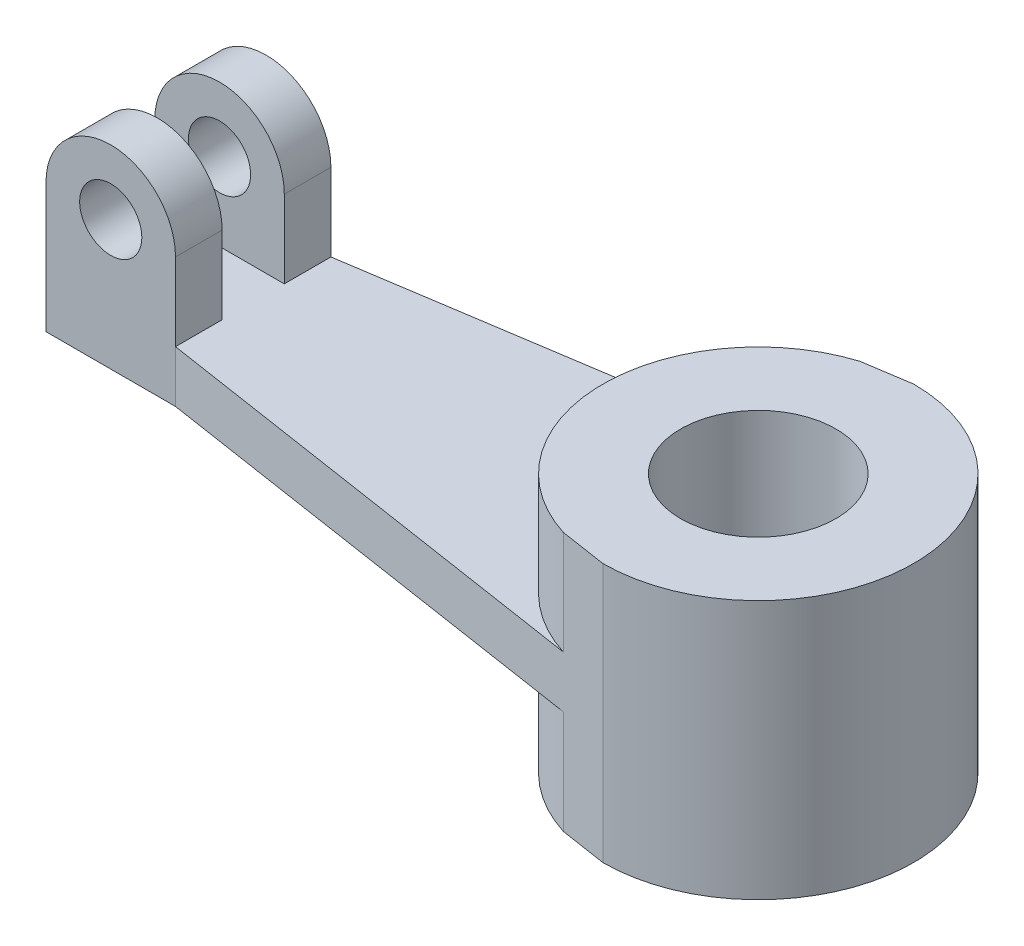
SolidWorks part; units mm, degrees
ref_plane "Front" through (0, 0, 0) normal (0, 0, 1) x (1, 0, 0)
ref_plane "Top" through (0, 0, 0) normal (0, 1, 0) x (1, 0, 0)
ref_plane "Right" through (0, 0, 0) normal (1, 0, 0) x (0, 0, -1)
sketch "Sketch1" plane through (0, 0, 0) normal (0, 1, 0) x (1, 0, 0)
  line L0 (-97.5, 15) -> (-122.5, 15)
  line L1 (-122.5, 15) -> (-122.5, -15)
  line L2 (-122.5, -15) -> (-97.5, -15)
  line L3 (-97.5, -15) -> (0, -30)
  line L4 (-97.5, 15) -> (0, 30)
  circle A0 centre (0, 0) radius 30
  point P4 (0, 0)
  point P9 (0, 0)
  point P10 (0, 0)
  point P11 (0, 0)
  point P13 (0, 30)
  point P14 (0, 0)
  point P15 (-110, 15)
  point P16 (-97.5, 14.942)
  point P17 (-122.5, 0)
  dimension "D1" = 30
  dimension "D2" = 30
  dimension "D3" = 25
  dimension "D4" = 110
extrude "Boss-Extrude2" add sketch "Sketch1" along normal blind 10 contours A0 L4 L0 L1 L2 L3 | L3 A0 L4
sketch "Sketch3" plane through (0, 10, 0) normal (0, 1, 0) x (1, 0, 0)
  line L0 (-97.5, 15) -> (-97.5, 6)
  line L1 (-97.5, 6) -> (-122.5, 6)
  line L2 (-122.5, 15) -> (-122.5, -15) construction
  line L3 (-122.5, 6) -> (-122.5, 15)
  line L4 (-122.5, 15) -> (-97.5, 15)
  line L5 (-97.5, -15) -> (-97.5, -6)
  line L6 (-97.5, -6) -> (-122.5, -6)
  line L7 (-122.5, -6) -> (-122.5, -15)
  line L8 (-122.5, -15) -> (-97.5, -15)
  circle A0 centre (0, 0) radius 30
  line M10 (-97.5, -15) -> (0, -30)
  arc M11 (0, -30) -> (0, 30) centre (0, 0) ccw
  line M12 (0, 30) -> (-97.5, 15)
  dimension "D1" = 9
  dimension "D2" = 9
extrude "Boss-Extrude3" add sketch "Sketch3" along normal blind 20 and the other way blind 30 contours A0 M12 M10 M11
sketch "Sketch4" plane through (0, 30, 0) normal (0, 1, 0) x (1, 0, 0)
  circle A0 centre (0, 0) radius 15
  dimension "D1" = 30
extrude "Cut-Extrude1" cut sketch "Sketch4" against normal through all
sketch "Sketch5" plane through (0, 10, 0) normal (0, 1, 0) x (1, 0, 0)
  line L0 (-122.5, 6) -> (-97.5, 6)
  line L1 (-97.5, 6) -> (-97.5, 15)
  line L2 (-97.5, 15) -> (-122.5, 15)
  line L3 (-122.5, 15) -> (-122.5, 6)
  line L4 (-122.5, -6) -> (-97.5, -6)
  line L5 (-97.5, -6) -> (-97.5, -15)
  line L6 (-97.5, -15) -> (-122.5, -15)
  line L7 (-122.5, -15) -> (-122.5, -6)
extrude "Boss-Extrude4" add sketch "Sketch5" along normal blind 15
sketch "Sketch6" plane through (0, 0, 15) normal (0, 0, 1) x (1, 0, 0)
  line L0 (-122.5, 25) -> (-97.5, 25) construction
  line L2 (-122.5, 25) -> (-97.5, 25)
  line L7 (-122.5, 0) -> (-97.5, 0)
  line L8 (-97.5, 0) -> (-97.5, 10)
  line L9 (-97.5, 10) -> (-97.5, 25)
  line L10 (-97.5, 25) -> (-122.5, 25)
  line L11 (-122.5, 25) -> (-122.5, 0)
  line L12 (-122.5, 0) -> (-97.5, 0)
  line L13 (-97.5, 0) -> (-97.5, 10)
  line L14 (-97.5, 10) -> (-97.5, 25)
  line L16 (-122.5, 25) -> (-122.5, 0)
  arc A0 (-122.5, 25) -> (-97.5, 25) centre (-110, 25) cw
  line M9 (-97.5, 25) -> (-122.5, 25)
  dimension "D1" = 0
extrude "Boss-Extrude5" add sketch "Sketch6" against normal blind 9 contours A0 M9
sketch "Sketch7" plane through (0, 0, -15) normal (0, 0, -1) x (-1, 0, 0)
  line L0 (97.5, 25) -> (122.5, 25) construction
  line L1 (97.5, 25) -> (122.5, 25)
  arc A0 (97.5, 25) -> (122.5, 25) centre (110, 25) cw
  arc A1 (122.5, 25) -> (97.5, 25) centre (110, 25) ccw construction
extrude "Boss-Extrude6" add sketch "Sketch7" against normal blind 9
sketch "Sketch8" plane through (0, 0, 15) normal (0, 0, 1) x (1, 0, 0)
  circle A0 centre (-110, 25) radius 6
  dimension "D1" = 12
extrude "Cut-Extrude2" cut sketch "Sketch8" against normal through all
